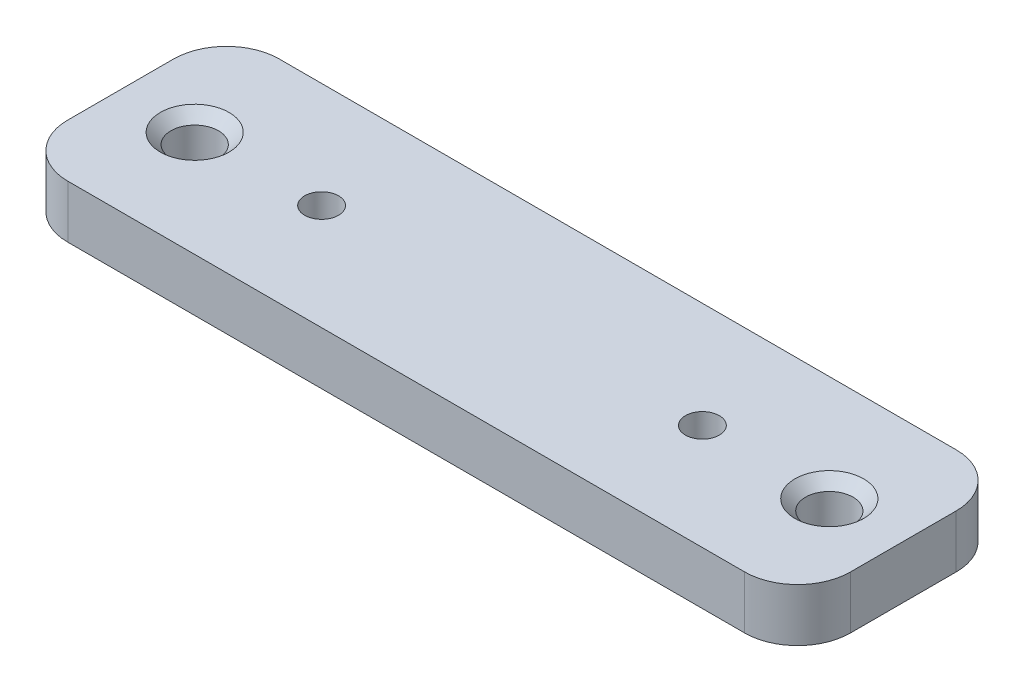
SolidWorks part; units mm, degrees
material "PBT Общее назначение"
ref_plane "Спереди" through (0, 0, 0) normal (0, 0, 1) x (1, 0, 0)
ref_plane "Сверху" through (0, 0, 0) normal (0, 1, 0) x (1, 0, 0)
ref_plane "Справа" through (0, 0, 0) normal (1, 0, 0) x (0, 0, -1)
sketch "Эскиз1" plane through (0, 0, 0) normal (0, 1, 0) x (1, 0, 0)
  line L0 (0, 0) -> (74, 0)
  line L1 (0, 0) -> (0, 20)
  line L2 (74, 0) -> (74, 20)
  line L3 (0, 20) -> (74, 20)
  line L4 (0, 10) -> (74, 10) construction
  line L5 (37, 20) -> (37, 0) construction
  line L6 (19, 8.4) -> (55, 8.4) construction
  line L7 (7, 7.75) -> (67, 7.75) construction
  circle A0 centre (19, 10) radius 1.6
  circle A1 centre (55, 10) radius 1.6
  circle A2 centre (7, 10) radius 2.25
  circle A3 centre (67, 10) radius 2.25
  point P15 (37, 8.4)
  point P22 (37, 7.75)
  dimension "D3" = 36
  dimension "D4" = 3.2
  dimension "D5" = 4.5
  dimension "D6" = 7
  dimension "D7" = 12
  dimension "D1" = 20
  dimension "D2" = 74
extrude "Бобышка-Вытянуть1" add sketch "Эскиз1" along normal blind 5
fillet "Скругление2" radius 5 4 edges at (0, 2.5, -20) (0, 2.5, 0) (74, 2.5, -20) (74, 2.5, 0)
chamfer "Фаска1" distance 1 angle 45 2 edges at (67, 5, -7.75) (7, 5, -7.75)
chamfer "Фаска2" distance 1 angle 45 2 edges at (55, 0, -8.4) (19, 0, -8.4)
